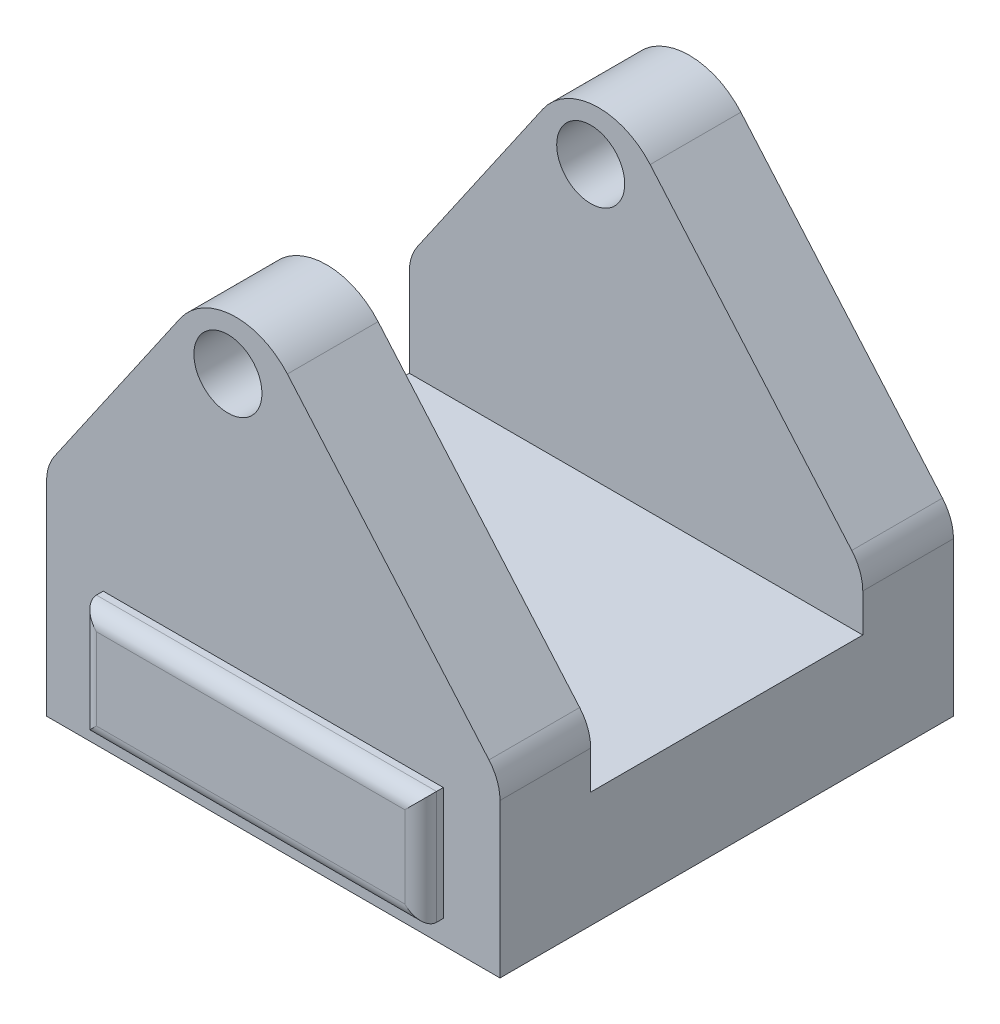
SolidWorks part; units mm, degrees
other "Markup1"
sketch "Sketch10" plane through (100, 194.2139, 110) normal (0.3708, 0.5736, 0.7304) x (0.8917, 0, -0.4526)
other "Markup2"
sketch "Sketch11" plane through (100, 194.2139, 110) normal (0.3708, 0.5736, 0.7304) x (0.8917, 0, -0.4526)
material "Tungsten"
ref_plane "Front Plane" through (0, 0, 0) normal (0, 0, 1) x (1, 0, 0)
ref_plane "Top Plane" through (0, 0, 0) normal (0, 1, 0) x (1, 0, 0)
ref_plane "Right Plane" through (0, 0, 0) normal (1, 0, 0) x (0, 0, -1)
sketch "Sketch1" plane through (0, 0, 0) normal (0, 1, 0) x (1, 0, 0)
  line L1 (-100, -100) -> (100, -100)
  line L2 (-100, -100) -> (-100, 100)
  line L3 (-100, 100) -> (100, 100)
  line L4 (100, -100) -> (100, 100)
  line L5 (-100, -100) -> (100, 100) construction
  line L6 (-100, 100) -> (100, -100) construction
  point P0 (0, 0)
  dimension "D1" = 200
  dimension "D2" = 200
extrude "Boss-Extrude1" add sketch "Sketch1" along normal blind 300
sketch "Sketch2" plane through (0, 0, 0) normal (0, -1, 0) x (1, 0, 0)
  circle A0 centre (0, 0) radius 75
  dimension "D1" = 150
extrude "Cut-Extrude1" cut sketch "Sketch2" against normal blind 50
sketch "Sketch3" plane through (0, 0, 100) normal (0, 0, 1) x (1, 0, 0)
  line L0 (-100, 95.9807) -> (-19.136, 213.1886)
  line L1 (-100, 300) -> (-100, 0) construction
  line L2 (-19.136, 213.1886) -> (100, 75.25)
  line L3 (100, 300) -> (100, 0) construction
  line L4 (100, 75.25) -> (100, 300)
  line L5 (100, 300) -> (-100, 300)
  line L6 (-100, 300) -> (-100, 95.9807)
extrude "Cut-Extrude2" cut sketch "Sketch3" against normal through all
fillet "Fillet1" radius 30 1 edges at (-19.136, 213.1886, 0)
fillet "Fillet2" radius 20 2 edges at (100, 75.25, 0) (-100, 95.9807, 0)
ref_plane "Plane1" through (0, 200, 0) normal (0, 1, 0) x (1, 0, 0)
sketch "Sketch4" plane through (0, 200, 0) normal (0, 1, 0) x (1, 0, 0)
  line L0 (100, 100) -> (100, -100) construction
  line L1 (-100, 60) -> (100, 60)
  line L2 (-100, 60) -> (-100, -60)
  line L3 (-100, -60) -> (100, -60)
  line L4 (100, 60) -> (100, -60)
  line L5 (-100, 60) -> (100, -60) construction
  line L6 (-100, -60) -> (100, 60) construction
  point P0 (0, 0)
  dimension "D1" = 120
extrude "Cut-Extrude3" cut sketch "Sketch4" against normal blind 149
sketch "Sketch7" plane through (0, 0, 60) normal (0, 0, -1) x (-1, 0, 0)
  line L1 (-100, 51) -> (-100, 67.8088) construction
  circle A0 centre (20, 170.7849) radius 15
  point P4 (0, 0)
  dimension "D1" = 30
  dimension "D2" = 120
extrude "Cut-Extrude4" cut sketch "Sketch7" against normal blind 149 and the other way blind 200
sketch "Sketch8" plane through (0, 0, 100) normal (0, 0, 1) x (1, 0, 0)
  line L1 (-75, 60.2601) -> (75, 60.2601)
  line L2 (-75, 60.2601) -> (-75, 10.2601)
  line L3 (-75, 10.2601) -> (75, 10.2601)
  line L4 (75, 60.2601) -> (75, 10.2601)
  point P4 (0, 10.2601)
  dimension "D1" = 150
  dimension "D2" = 50
extrude "Boss-Extrude2" add sketch "Sketch8" along normal blind 10
fillet "Fillet3" radius 7 4 edges at (0, 60.2601, 110) (75, 35.2601, 110) (0, 10.2601, 110) (-75, 35.2601, 110)
sketch "Sketch9" plane through (0, 0, -100) normal (0, 0, -1) x (-1, 0, 0)
  line L0 (-100, 67.8088) -> (-100, 0) construction
  line L1 (-75, 60.002) -> (75, 60.002)
  line L2 (-75, 60.002) -> (-75, 10.002)
  line L3 (-75, 10.002) -> (75, 10.002)
  line L4 (75, 60.002) -> (75, 10.002)
  line L5 (100, 89.7509) -> (100, 0) construction
  dimension "D1" = 150
  dimension "D2" = 50
  dimension "D3" = 25
  dimension "D4" = 25
extrude "Boss-Extrude3" add sketch "Sketch9" along normal blind 10
fillet "Fillet4" radius 7 4 edges at (0, 60.002, -110) (-75, 35.002, -110) (0, 10.002, -110) (75, 35.002, -110)
